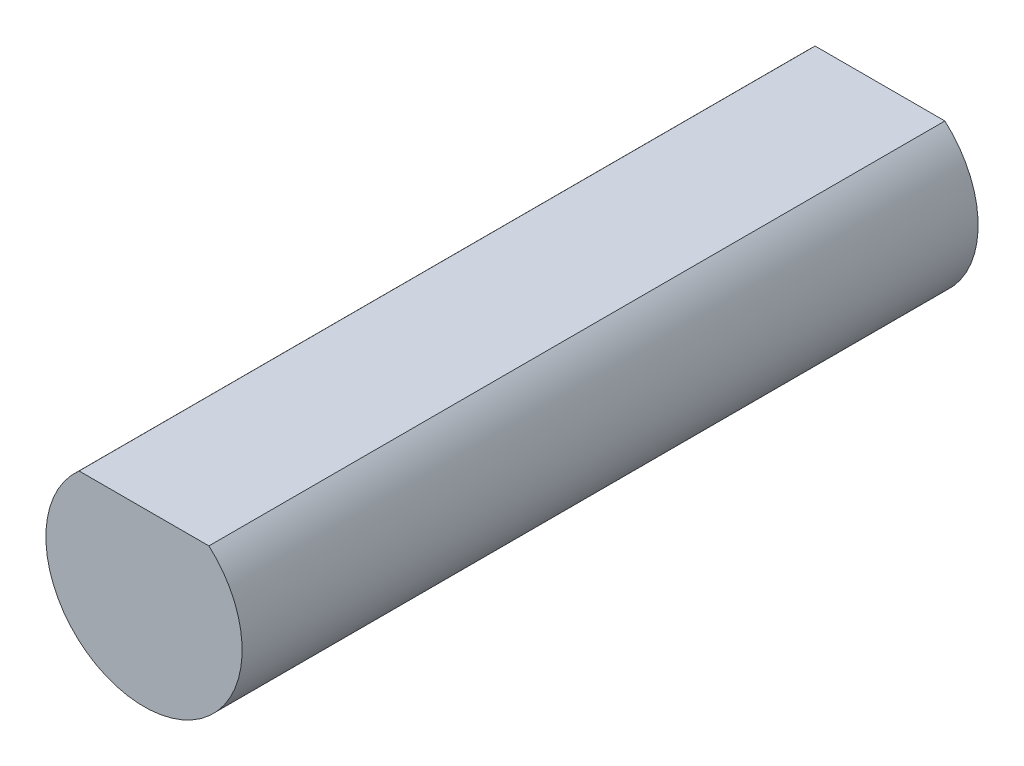
SolidWorks part; units mm, degrees
ref_plane "Front Plane" through (0, 0, 0) normal (0, 0, 1) x (1, 0, 0)
ref_plane "Top Plane" through (0, 0, 0) normal (0, 1, 0) x (1, 0, 0)
ref_plane "Right Plane" through (0, 0, 0) normal (1, 0, 0) x (0, 0, -1)
sketch "Sketch1" plane through (0, 0, 0) normal (0, 0, 1) x (1, 0, 0)
  line L0 (-1.3229, 1.5) -> (1.3229, 1.5)
  arc A0 (-1.3229, 1.5) -> (1.3229, 1.5) centre (0, 0) ccw
  dimension "D1" = 4
  dimension "D2" = 1.5
extrude "Boss-Extrude1" add sketch "Sketch1" along normal blind 15
